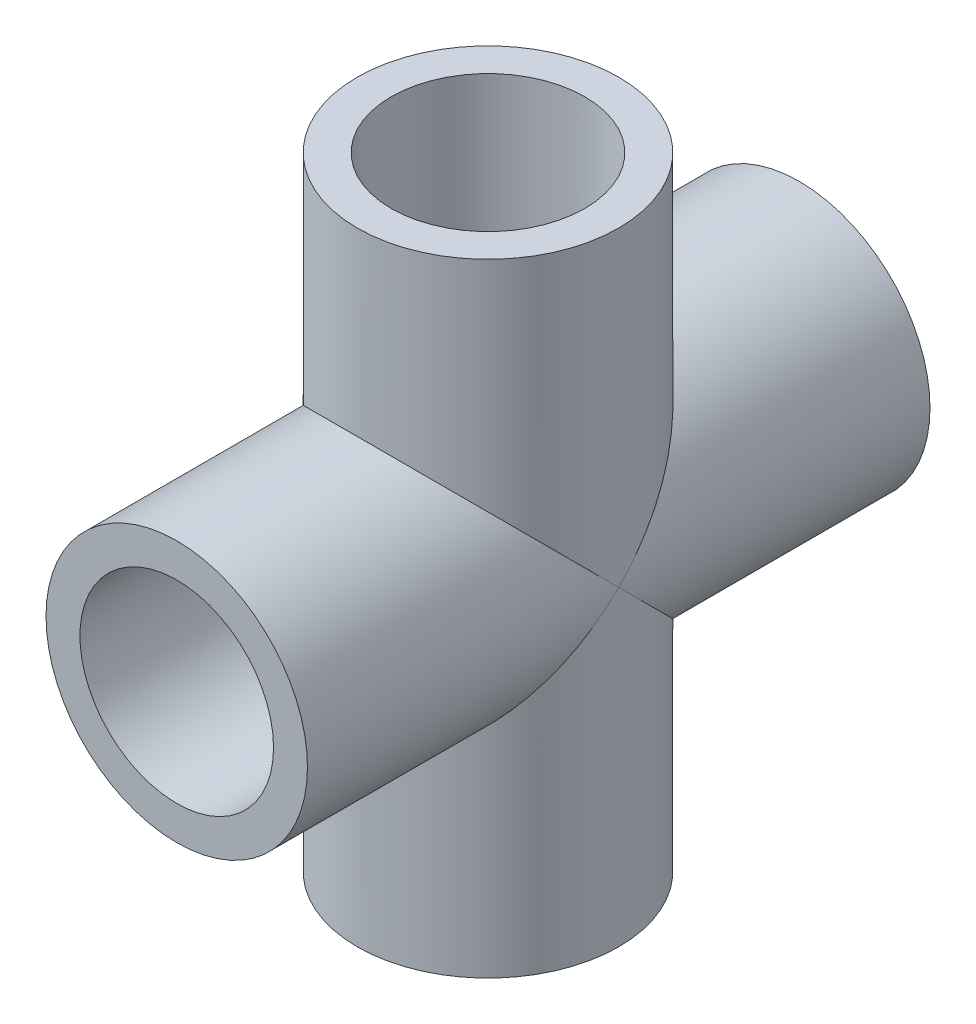
SolidWorks part; units mm, degrees
material "PVC Rigid"
ref_plane "Front Plane" through (0, 0, 0) normal (0, 0, 1) x (1, 0, 0)
ref_plane "Top Plane" through (0, 0, 0) normal (0, 1, 0) x (1, 0, 0)
ref_plane "Right Plane" through (0, 0, 0) normal (1, 0, 0) x (0, 0, -1)
sketch "Sketch1" plane through (0, 0, 0) normal (0, 0, 1) x (1, 0, 0)
  circle A0 centre (0, 0) radius 10.668
  circle A2 centre (0, 0) radius 7.8994
  dimension "D1" = 21.336
  dimension "D2" = 15.7988
extrude "Boss-Extrude1" add sketch "Sketch1" along normal blind 50.8
sketch "Sketch2" plane through (0, 0, 0) normal (0, 1, 0) x (1, 0, 0)
  line L0 (-10.668, -25.4) -> (10.668, -25.4) construction
  line L1 (-10.668, 0) -> (-10.668, -50.8) construction
  line L2 (10.668, -50.8) -> (10.668, 0) construction
  line L3 (0, 0) -> (0, -50.8) construction
  line L4 (-10.668, -50.8) -> (10.668, -50.8) construction
  circle A0 centre (0, -25.4) radius 10.668
  circle A1 centre (0, -25.4) radius 7.8994
  point P15 (0, -25.4)
  dimension "D1" = 21.336
  dimension "D2" = 15.7988
extrude "Boss-Extrude2" add sketch "Sketch2" along normal mid plane 50.8
sketch "Sketch3" plane through (0, 0, 50.8) normal (0, 0, 1) x (1, 0, 0)
  circle A0 centre (0, 0) radius 7.8994
extrude "Cut-Extrude1" cut sketch "Sketch3" against normal through all
sketch "Sketch4" plane through (0, 25.4, 0) normal (0, 1, 0) x (1, 0, 0)
  circle A0 centre (0, -25.4) radius 7.8994
extrude "Cut-Extrude2" cut sketch "Sketch4" against normal through all both and the other way through all
